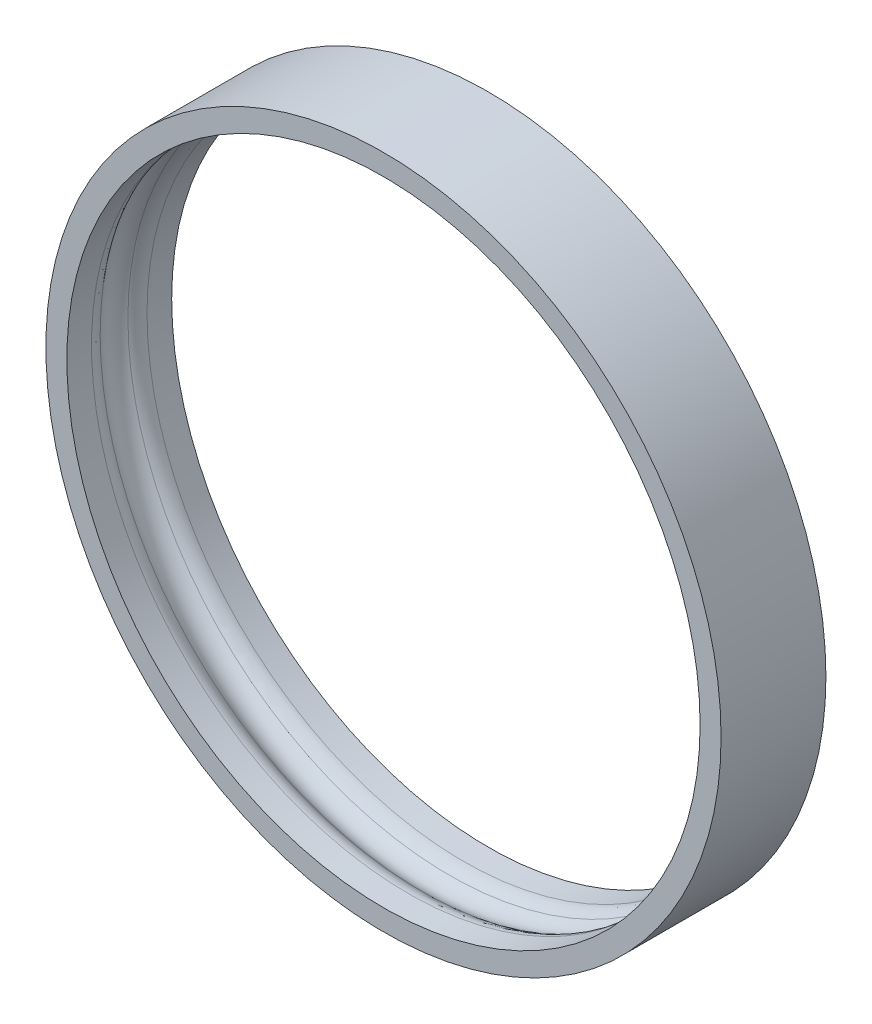
SolidWorks part; units mm, degrees
ref_plane "前视基准面" through (0, 0, 0) normal (0, 0, 1) x (1, 0, 0)
ref_plane "上视基准面" through (0, 0, 0) normal (0, 1, 0) x (1, 0, 0)
ref_plane "右视基准面" through (0, 0, 0) normal (1, 0, 0) x (0, 0, -1)
sketch "草图1" plane through (0, 0, 0) normal (0, 0, 1) x (1, 0, 0)
  circle A0 centre (0, 0) radius 15.1
  circle A1 centre (0, 0) radius 16.1
  dimension "D1" = 32.2
  dimension "D2" = 30.2
extrude "凸台-拉伸1" add sketch "草图1" along normal mid plane 5
sketch "草图3" plane through (0, 0, 0) normal (0, 1, 0) x (1, 0, 0)
  circle A0 centre (-14.6, 0) radius 1
  dimension "D1" = 2
  dimension "D2" = 14.6
revolve "切除-旋转1" cut sketch "草图3" angle 360 about axis through (0, 0, 2.5) along (0, 0, -1)
fillet "圆角1" radius 1 2 edges at (-15.1, 0, 0.866) (15.1, 0, -0.866)
equation "\"d\"= 32.2"
equation "\"D1@草图1\"=\"d\""
equation "\"d2\"= \"d\" - 2"
equation "\"D2@草图1\"=\"d2\""
equation "\"l1\"= \"d2\" / 2 - 0.5"
equation "\"D2@草图3\"=\"l1\""
